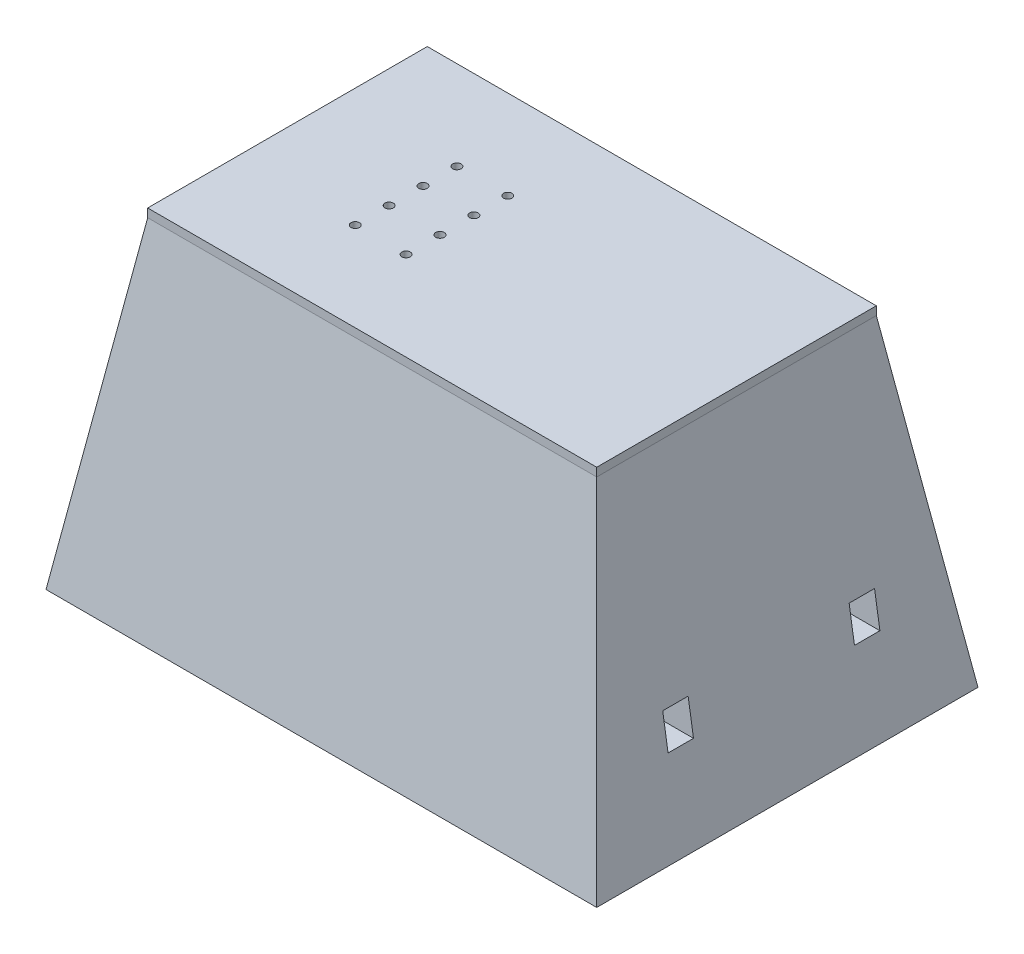
SolidWorks part; units mm, degrees
ref_plane "Front Plane" through (0, 0, 0) normal (0, 0, 1) x (1, 0, 0)
ref_plane "Top Plane" through (0, 0, 0) normal (0, 1, 0) x (1, 0, 0)
ref_plane "Right Plane" through (0, 0, 0) normal (1, 0, 0) x (0, 0, -1)
sketch "Sketch2" plane through (0, 0, 0) normal (0, 1, 0) x (1, 0, 0)
  line L0 (0, 0) -> (-35, 0) construction
  line L1 (0, 0) -> (255, 0)
  line L2 (0, 0) -> (0, 155)
  line L3 (0, 155) -> (255, 155)
  line L4 (255, 0) -> (255, 155)
  line L5 (-35, -35) -> (290, -35)
  line L6 (-35, -35) -> (-35, 190)
  line L7 (-35, 190) -> (290, 190)
  line L8 (290, -35) -> (290, 190)
  line L9 (255, 0) -> (290, 0) construction
  line L10 (0, 0) -> (0, -35) construction
  line L11 (0, 155) -> (0, 190) construction
  dimension "D1" = 255
  dimension "D2" = 155
  dimension "D3" = 35
ref_plane "Plane1" through (0, 190, 0) normal (0, 1, 0) x (1, 0, 0)
sketch "Sketch4" plane through (0, 190, 0) normal (0, 1, 0) x (1, 0, 0)
  line L0 (255, 155) -> (260, 155) construction
  line L1 (-5, 160) -> (260, 160)
  line L2 (-5, 160) -> (-5, -5)
  line L3 (-5, -5) -> (260, -5)
  line L4 (260, 160) -> (260, -5)
  line L5 (0, 155) -> (255, 155)
  line L6 (0, 155) -> (0, 0)
  line L7 (0, 0) -> (255, 0)
  line L8 (255, 155) -> (255, 0)
  line L9 (255, 155) -> (255, 160) construction
  line L10 (255, 0) -> (255, -5) construction
  line L11 (0, 0) -> (-5, 0) construction
  point P10 (0, 0)
  point P15 (0, 0)
  point P17 (0, 0)
  point P19 (0, 0)
  point P21 (0, 0)
  point P23 (0, 0)
  point P24 (0, 0)
  point P25 (0, 0)
  point P26 (0, 0)
  dimension "D1" = 5
ref_plane "Plane2" through (0, 0, 0) normal (1, 0, 0) x (0, 0, -1)
ref_plane "Plane3" through (-34.1486, 5.3919, 0) normal (-0.9878, 0.156, 0) x (0, 0, 1)
loft "Loft2" add section "Sketch2" section "Sketch4"
sketch "Sketch8" plane through (0, 190, 0) normal (0, 1, 0) x (1, 0, 0)
  line L1 (0, 0) -> (255, 0)
  line L2 (0, 0) -> (0, 155)
  line L3 (0, 155) -> (255, 155)
  line L4 (255, 0) -> (255, 155)
sketch "Sketch9" plane through (0, 0, 0) normal (0, -1, 0) x (1, 0, 0)
  line L1 (0, 0) -> (255, 0)
  line L2 (0, 0) -> (0, -155)
  line L3 (0, -155) -> (255, -155)
  line L4 (255, 0) -> (255, -155)
loft "Cut-Loft1" cut profiles "Sketch8", "Sketch9"
sketch "Sketch10" plane through (0, 190, 0) normal (0, 1, 0) x (1, 0, 0)
  line L1 (-5, 160) -> (260, 160)
  line L2 (-5, 160) -> (-5, -5)
  line L3 (-5, -5) -> (260, -5)
  line L4 (260, 160) -> (260, -5)
extrude "Boss-Extrude1" add sketch "Sketch10" along normal blind 5
ref_plane "Plane4" through (0, 33, 0) normal (0, 1, 0) x (1, 0, 0)
sketch "Sketch13" plane through (0, 33, 0) normal (0, 1, 0) x (1, 0, 0)
  line L1 (0, 0) -> (255, 0) construction
  line L2 (0, 0) -> (0, 155) construction
  line L3 (0, 155) -> (255, 155) construction
  line L4 (255, 0) -> (255, 155) construction
  line L5 (0, 155) -> (10, 155)
  line L6 (0, 155) -> (0, 145)
  line L7 (0, 145) -> (10, 145)
  line L8 (10, 155) -> (10, 145)
  line L9 (255, 155) -> (245, 155)
  line L10 (255, 155) -> (255, 145)
  line L11 (255, 145) -> (245, 145)
  line L12 (245, 155) -> (245, 145)
  line L13 (255, 0) -> (245, 0)
  line L14 (255, 0) -> (255, 10)
  line L15 (255, 10) -> (245, 10)
  line L16 (245, 0) -> (245, 10)
  line L17 (0, 0) -> (10, 0)
  line L18 (0, 0) -> (0, 10)
  line L19 (0, 10) -> (10, 10)
  line L20 (10, 0) -> (10, 10)
  dimension "D1" = 10
extrude "Boss-Extrude2" add sketch "Sketch13" along normal up to surface (162 mm away) up to face at (127.5, 195, -77.5)
sketch "Sketch14" plane through (0, 195, 0) normal (0, 1, 0) x (1, 0, 0)
  line L0 (255, 155) -> (255, 160) construction
  line L1 (0, 0) -> (255, 0) construction
  line L2 (0, 0) -> (0, 155) construction
  line L3 (0, 155) -> (255, 155) construction
  line L4 (255, 0) -> (255, 155) construction
  line L5 (260, 160) -> (-5, 160) construction
  line L6 (0, 0) -> (0, -5) construction
  line L7 (-5, -5) -> (260, -5) construction
  line L8 (255, 155) -> (260, 155) construction
  line L9 (260, -5) -> (260, 160) construction
  line L10 (0, 77.5) -> (255, 77.5) construction
  circle A0 centre (65, 47.5) radius 2.5
  circle A1 centre (65, 67.5) radius 2.5
  circle A2 centre (95, 67.5) radius 2.5
  circle A3 centre (95, 47.5) radius 2.5
  circle A4 centre (95, 107.5) radius 2.5
  circle A5 centre (95, 87.5) radius 2.5
  circle A6 centre (65, 87.5) radius 2.5
  circle A7 centre (65, 107.5) radius 2.5
  dimension "D3" = 5
  dimension "D1" = 20
  dimension "D2" = 30
  dimension "D4" = 10
  dimension "D5" = 65
extrude "Cut-Extrude1" cut sketch "Sketch14" against normal through all
ref_plane "Plane5" through (290, 0, 0) normal (1, 0, 0) x (0, 0, -1)
sketch "Sketch15" plane through (290, 0, 0) normal (1, 0, 0) x (0, 0, -1)
  line L0 (0, 0) -> (0, 190) construction
  line L1 (160, 190) -> (-5, 190) construction
  line L2 (0, 50) -> (15, 50) construction
  line L3 (15, 50) -> (30, 50)
  line L4 (15, 50) -> (15, 70)
  line L5 (15, 70) -> (30, 70)
  line L6 (30, 70) -> (30, 50)
  line L7 (-35, 0) -> (190, 0) construction
  line L8 (77.5, 0) -> (77.5, 190) construction
  line L9 (140, 70) -> (125, 70)
  line L10 (140, 50) -> (140, 70)
  line L11 (140, 50) -> (125, 50)
  line L12 (125, 70) -> (125, 50)
  dimension "D1" = 15
  dimension "D2" = 50
  dimension "D3" = 20
extrude "Cut-Extrude2" cut sketch "Sketch15" against normal up to next
